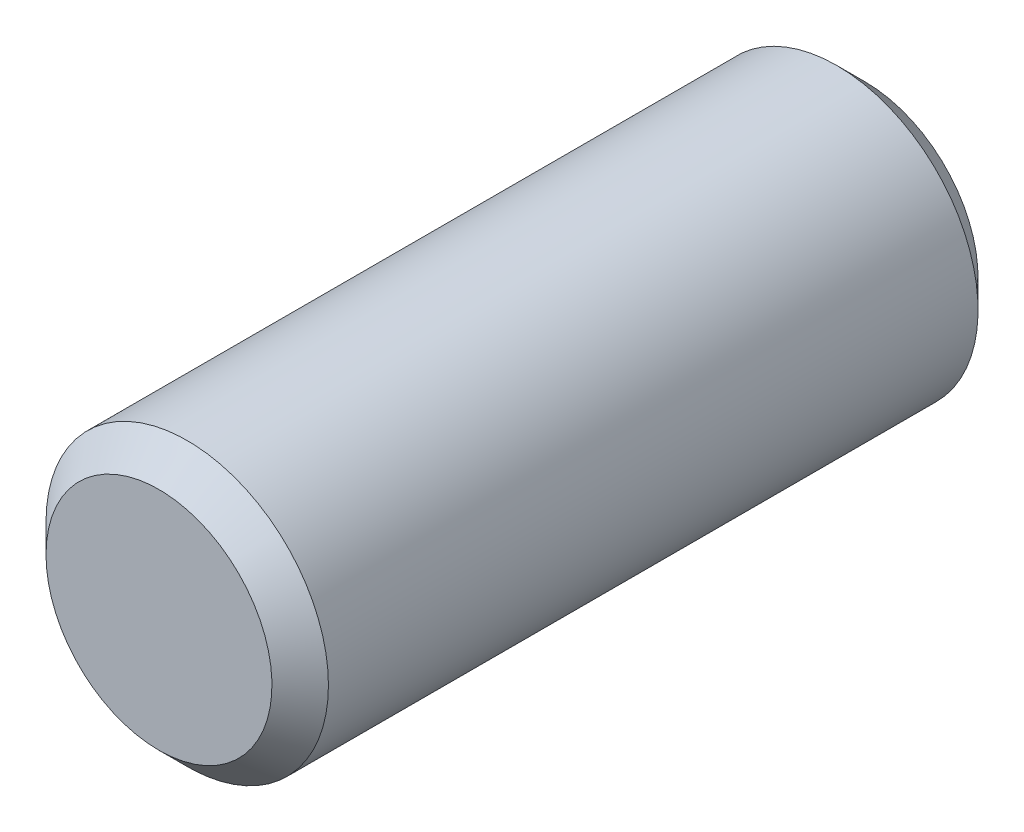
SolidWorks part; units mm, degrees
ref_plane "Plan de face" through (0, 0, 0) normal (0, 0, 1) x (1, 0, 0)
ref_plane "Plan de dessus" through (0, 0, 0) normal (0, 1, 0) x (1, 0, 0)
ref_plane "Plan de droite" through (0, 0, 0) normal (1, 0, 0) x (0, 0, -1)
sketch "Esquisse1" plane through (0, 0, 0) normal (1, 0, 0) x (0, 0, -1)
  line L1 (1.25, 0.25) -> (-1.25, 0.25)
  line L2 (1.25, 0.25) -> (1.25, -0.25)
  line L3 (1.25, -0.25) -> (-1.25, -0.25)
  line L4 (-1.25, 0.25) -> (-1.25, -0.25)
  line L5 (1.25, 0.25) -> (-1.25, -0.25) construction
  line L6 (1.25, -0.25) -> (-1.25, 0.25) construction
  point P0 (0, 0)
  dimension "D1" = 0.5
  dimension "D2" = 2.5
revolve "Révolution1" add sketch "Esquisse1" angle 360 about L3
chamfer "Chanfrein1" distance 0.1 angle 45 2 edges at (0, 0.25, -1.25) (0, 0.25, 1.25)
